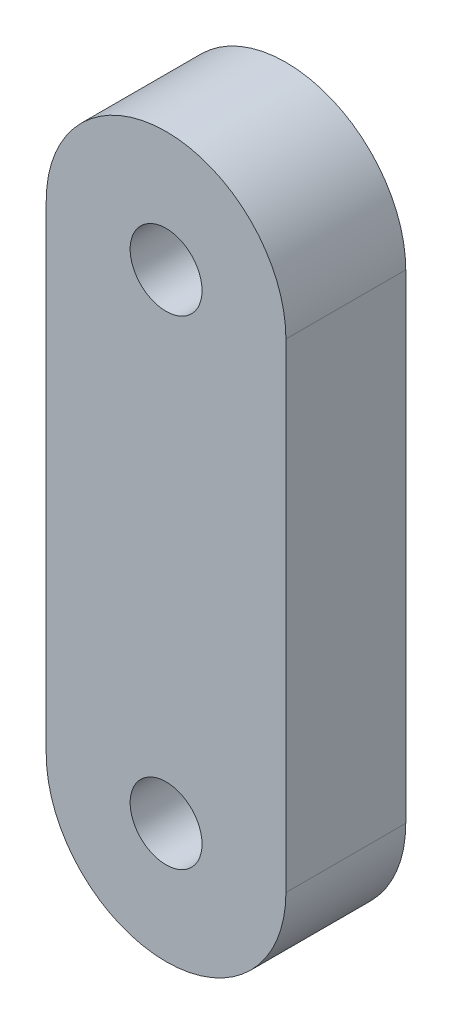
SolidWorks part; units mm, degrees
ref_plane "前视基准面" through (0, 0, 0) normal (0, 0, 1) x (1, 0, 0)
ref_plane "上视基准面" through (0, 0, 0) normal (0, 1, 0) x (1, 0, 0)
ref_plane "右视基准面" through (0, 0, 0) normal (1, 0, 0) x (0, 0, -1)
sketch "草图1" plane through (0, 0, 0) normal (0, 0, 1) x (1, 0, 0)
  line L1 (-1, 2) -> (1, 2)
  line L2 (-1, 2) -> (-1, -2)
  line L3 (-1, -2) -> (1, -2)
  line L4 (1, 2) -> (1, -2)
  line L5 (-1, 2) -> (1, -2) construction
  line L6 (-1, -2) -> (1, 2) construction
  circle A0 centre (0, 2) radius 1
  circle A1 centre (0, -2) radius 1
  circle A2 centre (0, 2) radius 0.3
  circle A3 centre (0, -2) radius 0.3
  point P0 (0, 0)
extrude "凸台-拉伸1" add sketch "草图1" along normal blind 1 contours A2 L1 A0 | A2 L1 A0 | A1 L4 A0 L2 | A3 L3 A1 | A3 L3 A1
